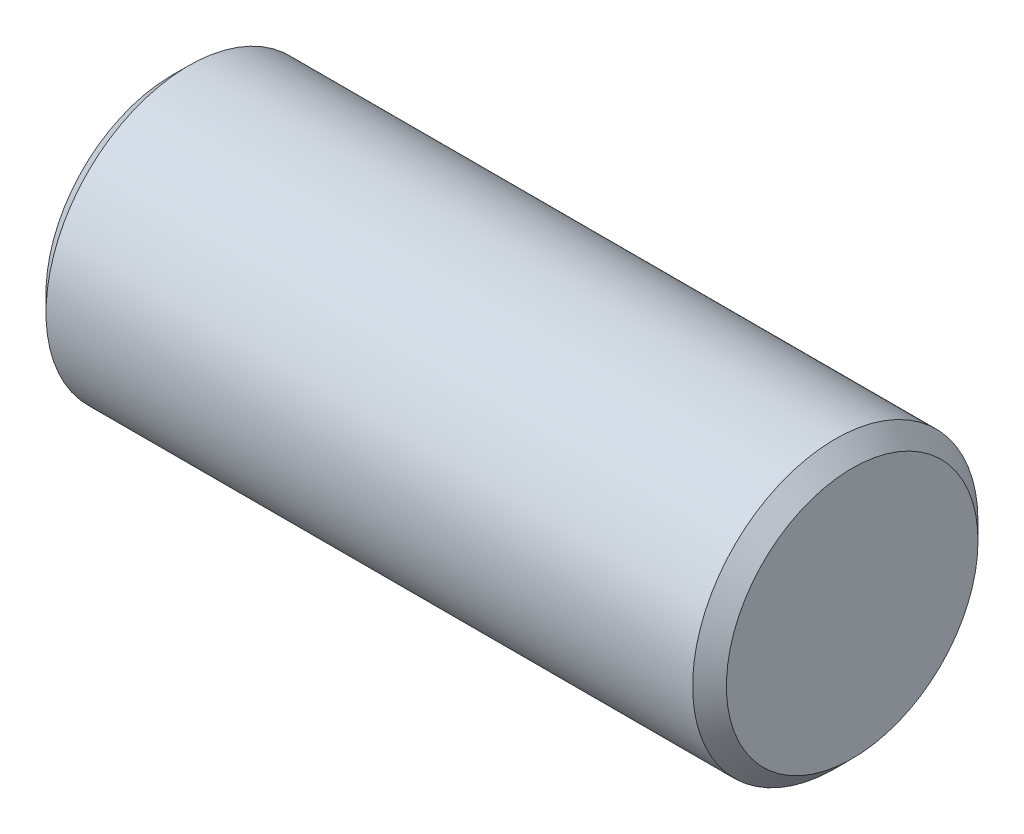
SolidWorks part; units mm, degrees
ref_plane "Front Plane" through (0, 0, 0) normal (0, 0, 1) x (1, 0, 0)
ref_plane "Top Plane" through (0, 0, 0) normal (0, 1, 0) x (1, 0, 0)
ref_plane "Right Plane" through (0, 0, 0) normal (1, 0, 0) x (0, 0, -1)
sketch "Sketch14" plane through (0, 0, 0) normal (1, 0, 0) x (0, 0, -1)
  circle A0 centre (0, 0) radius 16.9
  dimension "D1" = 33.8
extrude "Boss-Extrude1" add sketch "Sketch14" along normal blind 82
sketch "Sketch16" plane through (0, 0, 0) normal (0, 1, 0) x (1, 0, 0)
  line L2 (1.4142, 16.9) -> (1.4142, 0)
  line L6 (0, 0) -> (0, 15.4858)
  line L7 (0, 16.9) -> (0, -16.9) construction
  line L8 (1.4142, 16.9) -> (0, 15.4858)
  line L9 (0, 0) -> (1.4142, 0)
  point P0 (0, 0)
revolve "Cut-Revolve4" cut sketch "Sketch16" angle 360 about axis through (82, 0, 0) along (-1, 0, 0)
chamfer "Chamfer1" distance 2 angle 45 2 edges at (82, 0, -16.9) (1.4142, 0, -16.9)
